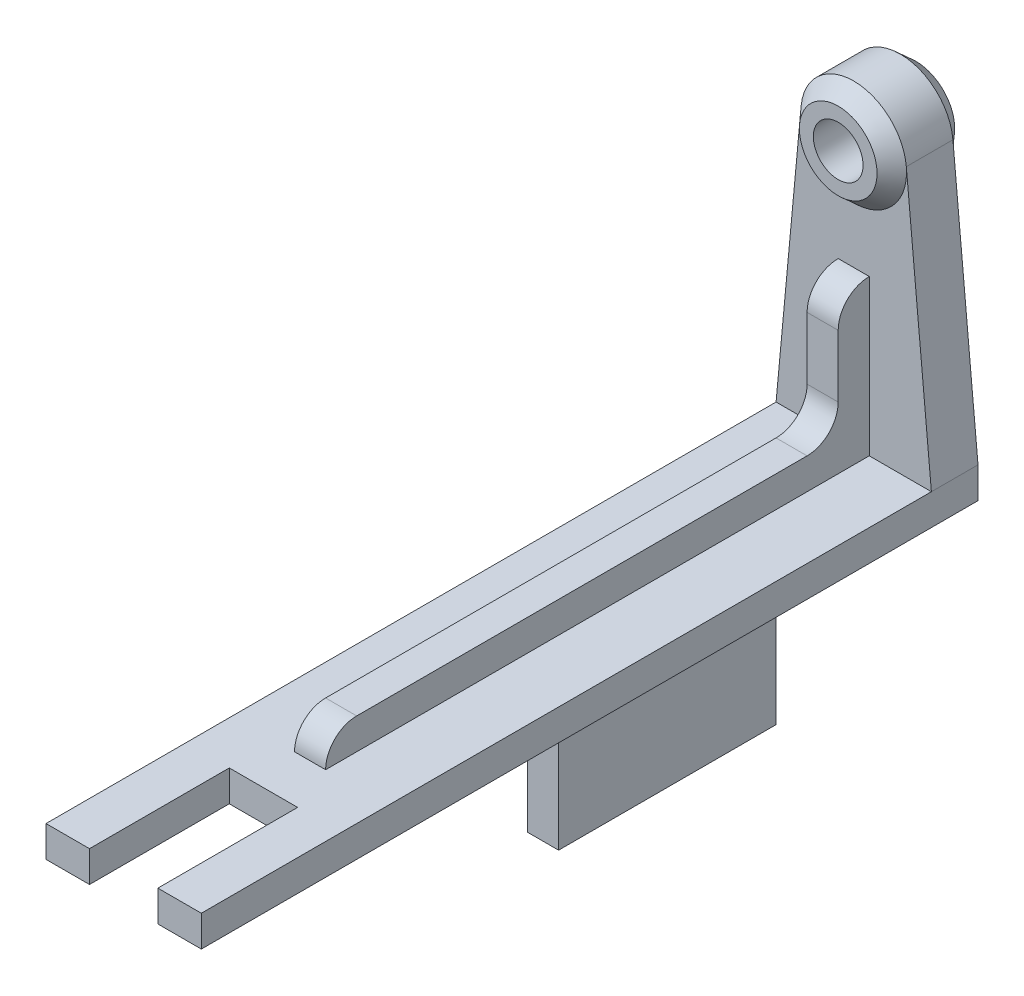
SolidWorks part; units mm, degrees
ref_plane "Front Plane" through (0, 0, 0) normal (0, 0, 1) x (1, 0, 0)
ref_plane "Top Plane" through (0, 0, 0) normal (0, 1, 0) x (1, 0, 0)
ref_plane "Right Plane" through (0, 0, 0) normal (1, 0, 0) x (0, 0, -1)
sketch "Sketch1" plane through (0, 0, 0) normal (0, 0, 1) x (1, 0, 0)
  line L0 (-25, -85) -> (-16.9266, 1.5784)
  line L2 (-25, -85) -> (-25, -95)
  line L3 (-25, -95) -> (25, -95)
  line L4 (25, -85) -> (25, -95)
  line L5 (-25, -85) -> (25, -95) construction
  line L6 (-25, -95) -> (25, -85) construction
  line L7 (25, -85) -> (16.9266, 1.5784)
  arc A0 (16.9266, 1.5784) -> (-16.9266, 1.5784) centre (0, 0) ccw
  point P3 (0, -90)
  dimension "D1" = 34
  dimension "D2" = 95
  dimension "D3" = 50
  dimension "D4" = 10
extrude "Boss-Extrude1" add sketch "Sketch1" along normal mid plane 15
sketch "Sketch2" plane through (0, 0, 7.5) normal (0, 0, 1) x (1, 0, 0)
  line L1 (-25, -95) -> (25, -95)
  line L2 (-25, -95) -> (-25, -85)
  line L3 (-25, -85) -> (25, -85)
  line L4 (25, -95) -> (25, -85)
extrude "Boss-Extrude2" add sketch "Sketch2" along normal blind 235
sketch "Sketch3" plane through (0, 0, 0) normal (1, 0, 0) x (0, 0, -1)
  line L0 (-1025, 0) -> (-12.5, 0) construction
  line L1 (0, 17) -> (0, 19.6331) construction
  line L2 (-12.5, 8) -> (-12.5, 12.5)
  line L3 (-12.5, 12.5) -> (-7.5, 17)
  line L4 (-7.5, 17) -> (-7.5, 8)
  line L5 (-12.5, 8) -> (-7.5, 8)
  line L6 (-7.5, 0) -> (50000, 0) construction
  line L8 (12.5, 8) -> (7.5, 8)
  line L9 (7.5, 17) -> (7.5, 8)
  line L10 (12.5, 12.5) -> (7.5, 17)
  line L11 (12.5, 8) -> (12.5, 12.5)
  dimension "D1" = 12.5
  dimension "D2" = 5
  dimension "D3" = 8
revolve "Revolve1" add sketch "Sketch3" angle 360 about L0
sketch "Sketch4" plane through (0, 0, 0) normal (1, 0, 0) x (0, 0, -1)
  line L0 (-17.5094, -45) -> (-17.5094, -65)
  line L1 (-27.5094, -75) -> (-172.5, -75)
  line L2 (-242.5, -95) -> (7.5, -95) construction
  line L3 (-242.5, -85) -> (-7.5, -85) construction
  line L4 (-7.5, -85) -> (-7.5, 1.5784) construction
  line L5 (-182.5, -85) -> (-7.5, -85)
  line L6 (-7.5, -85) -> (-7.5, -35)
  line L7 (-7.5094, -35) -> (-7.5, -35)
  line L8 (-107.5, -95) -> (-37.5, -95)
  line L9 (-107.5, -95) -> (-107.5, -144.9339)
  line L10 (-107.5, -144.9339) -> (-37.5, -144.9339)
  line L11 (-37.5, -95) -> (-37.5, -144.9339)
  line L12 (7.5, -85) -> (7.5, 1.5784) construction
  arc A0 (-172.5, -75) -> (-182.5, -85) centre (-172.5, -85) ccw
  arc A1 (-7.5094, -35) -> (-17.5094, -45) centre (-7.5094, -45) ccw
  arc A2 (-17.5094, -65) -> (-27.5094, -75) centre (-27.5094, -65) cw
  dimension "D1" = 10
  dimension "D2" = 10
  dimension "D3" = 10
  dimension "D4" = 50
  dimension "D5" = 10
  dimension "D6" = 175
  dimension "D7" = 70
  dimension "D8" = 45
extrude "Boss-Extrude3" add sketch "Sketch4" along normal mid plane 10
sketch "Sketch5" plane through (0, 0, 7.5) normal (0, 0, 1) x (1, 0, 0)
  circle A1 centre (0, 0) radius 8
  circle A2 centre (0, 0) radius 8
  dimension "D1" = 0
extrude "Cut-Extrude1" cut sketch "Sketch5" against normal through all
sketch "Sketch6" plane through (0, 0, 0) normal (1, 0, 0) x (0, 0, -1)
  line L0 (-107.5, -95) -> (-107.5, -144.9339) construction
  line L1 (-264.8074, -126.5423) -> (-197.5, -126.5423)
  line L2 (-264.8074, -126.5423) -> (-264.8074, -57.8028)
  line L3 (-264.8074, -57.8028) -> (-197.5, -57.8028)
  line L4 (-197.5, -126.5423) -> (-197.5, -57.8028)
  dimension "D1" = 90
extrude "Cut-Extrude2" cut sketch "Sketch6" against normal mid plane 22
